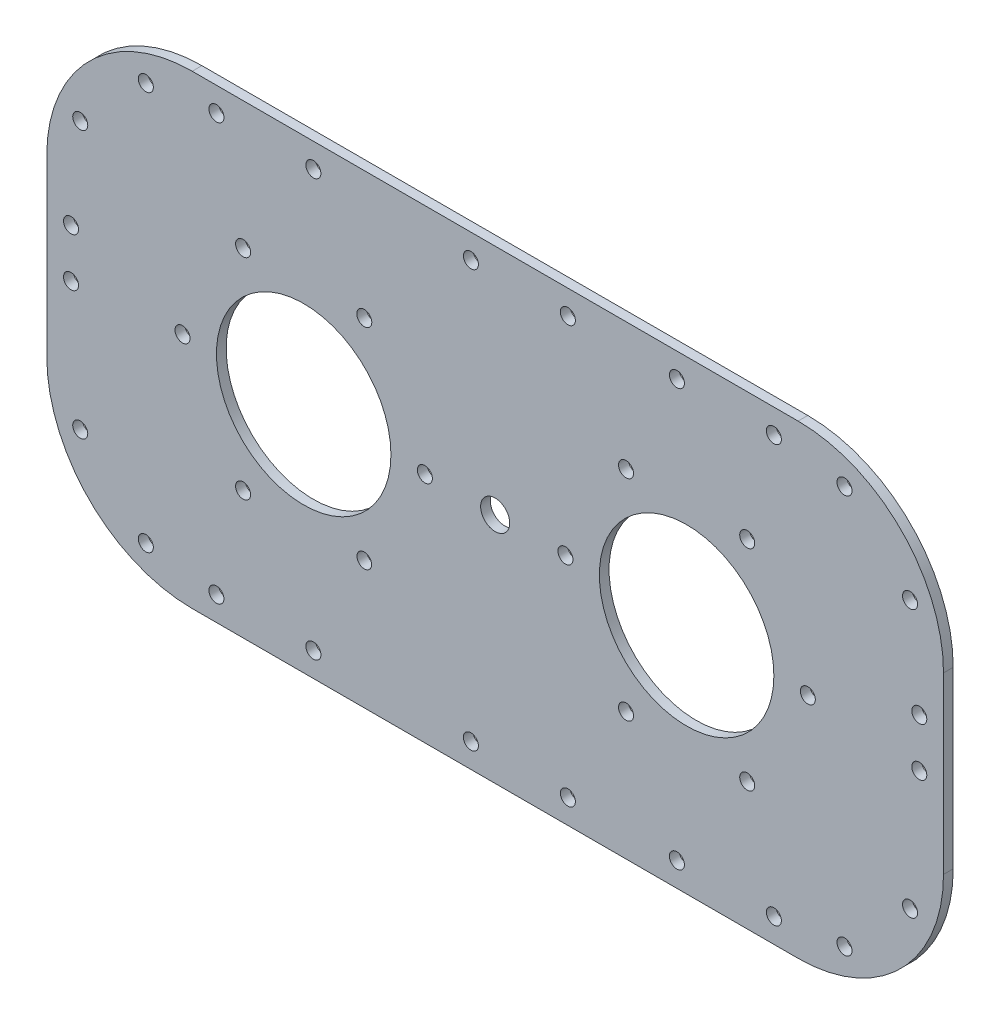
SolidWorks part; units mm, degrees
material "Thornel Mat VMA"
ref_plane "前视基准面" through (0, 0, 0) normal (0, 0, 1) x (1, 0, 0)
ref_plane "上视基准面" through (0, 0, 0) normal (0, 1, 0) x (1, 0, 0)
ref_plane "右视基准面" through (0, 0, 0) normal (1, 0, 0) x (0, 0, -1)
sketch "草图1" plane through (0, 0, 0) normal (0, 0, 1) x (1, 0, 0)
  line L0 (-39.5, 0) -> (39.5, 0) construction
  line L3 (-62.5, 48) -> (62.5, 48)
  line L4 (-92.5, 18) -> (-92.5, -18)
  line L5 (-62.5, -48) -> (62.5, -48)
  line L6 (92.5, 18) -> (92.5, -18)
  line L7 (-92.5, 48) -> (92.5, -48) construction
  line L8 (-92.5, -48) -> (92.5, 48) construction
  line L9 (-39.5, 0) -> (-52, -21.6506) construction
  line L10 (-39.5, 0) -> (-39.5, -25) construction
  line L11 (-52, 21.6506) -> (-27, -21.6506) construction
  line L12 (-39.5, 0) -> (-27, 21.6506) construction
  line L13 (39.5, 0) -> (27, -21.6506) construction
  line L14 (39.5, 0) -> (52, -21.6506) construction
  line L15 (39.5, 0) -> (39.5, -25) construction
  line L16 (39.5, 0) -> (52, 21.6506) construction
  line L17 (27, 21.6506) -> (39.5, 0) construction
  line L18 (39.5, 0) -> (64.5, 0) construction
  line L19 (-83.7132, 39.2132) -> (-62.5, 18) construction
  line L20 (-83.7132, -39.2132) -> (-73.5552, -29.0552) construction
  line L21 (83.7132, -39.2132) -> (62.5, -18) construction
  line L22 (83.7132, 39.2132) -> (66.1506, 21.6506) construction
  line L23 (62.5, -48) -> (62.5, 48) construction
  line L24 (-62.5, -48) -> (-62.5, 48) construction
  line L25 (0, 48) -> (0, -63.7675) construction
  line L26 (72.0671, 41.097) -> (62.5, 18) construction
  line L27 (-20, -40) -> (20, -40) construction
  line L28 (-20, -40) -> (-20, -46) construction
  line L29 (-20, -46) -> (20, -46) construction
  line L30 (20, -40) -> (20, -46) construction
  line L31 (-20, -40) -> (20, -46) construction
  line L32 (-20, -46) -> (20, -40) construction
  line L33 (62.5, 18) -> (85.597, 27.5671) construction
  line L34 (72.0671, -41.097) -> (62.5, -18) construction
  line L35 (62.5, -18) -> (85.597, -27.5671) construction
  line L36 (92.5, -18) -> (62.5, -18) construction
  line L37 (-73.5552, -29.0552) -> (-62.5, -18) construction
  line L38 (-62.5, -18) -> (-92.5, -18) construction
  line L39 (-85.597, -27.5671) -> (-62.5, -18) construction
  line L40 (-62.5, -18) -> (-72.0671, -41.097) construction
  line L41 (-85.597, 27.5671) -> (-62.5, 18) construction
  line L42 (-62.5, 18) -> (-72.0671, 41.097) construction
  circle A16 centre (-39.5, 0) radius 25 construction
  circle A17 centre (39.5, 0) radius 25 construction
  arc A18 (92.5, 18) -> (62.5, 48) centre (62.5, 18) ccw
  arc A19 (92.5, -18) -> (62.5, -48) centre (62.5, -18) cw
  arc A20 (-92.5, -18) -> (-62.5, -48) centre (-62.5, -18) ccw
  arc A21 (-92.5, 18) -> (-62.5, 48) centre (-62.5, 18) cw
  circle A22 centre (-64.5, 0) radius 1.55
  circle A23 centre (-14.5, 0) radius 1.55
  circle A24 centre (14.5, 0) radius 1.55
  circle A25 centre (64.5, 0) radius 1.55
  circle A26 centre (27, 21.6506) radius 1.55
  circle A27 centre (52, 21.6506) radius 1.55
  circle A28 centre (52, -21.6506) radius 1.55
  circle A29 centre (27, -21.6506) radius 1.55
  circle A30 centre (-52, -21.6506) radius 1.55
  circle A33 centre (-52, 21.6506) radius 1.55
  circle A34 centre (-27, -21.6506) radius 1.51
  circle A35 centre (-27, 21.6506) radius 1.55
  circle A48 centre (-39.5, 0) radius 18
  circle A49 centre (39.5, 0) radius 18
  circle A50 centre (57.5, -43) radius 1.55
  circle A51 centre (37.5, -43) radius 1.55
  circle A52 centre (-57.5, -43) radius 1.55
  circle A53 centre (-37.5, -43) radius 1.55
  circle A54 centre (-57.5, 43) radius 1.55
  circle A55 centre (-37.5, 43) radius 1.55
  circle A56 centre (37.5, 43) radius 1.55
  circle A57 centre (57.5, 43) radius 1.55
  circle A58 centre (15, -43) radius 1.55
  circle A59 centre (-5, -43) radius 1.55
  circle A60 centre (-5, 43) radius 1.55
  circle A61 centre (15, 43) radius 1.55
  circle A62 centre (85.597, 27.5671) radius 1.55
  circle A63 centre (72.0671, 41.097) radius 1.55
  circle A64 centre (72.0671, -41.097) radius 1.55
  circle A65 centre (85.597, -27.5671) radius 1.55
  circle A66 centre (-85.597, -27.5671) radius 1.55
  circle A67 centre (-72.0671, -41.097) radius 1.55
  circle A68 centre (-85.597, 27.5671) radius 1.55
  circle A69 centre (-72.0671, 41.097) radius 1.55
  point P0 (0, 0)
  point P9 (0, 0)
  point P51 (-39.5, 0)
  point P77 (0, -43)
  dimension "D2" = 96
  dimension "D4" = 30
  dimension "D5" = 30
  dimension "D6" = 30
  dimension "D8" = 30
  dimension "D12" = 5
  dimension "D20" = 5
  dimension "D16" = 5
  dimension "D30" = 5
  dimension "D32" = 22.5
  dimension "D34" = 25
  dimension "D36" = 22.5
  dimension "D40" = 22.5
  dimension "D44" = 22.5
  dimension "D1" = 79
  dimension "D3" = 185
  dimension "D7" = 60
  dimension "D9" = 30
  dimension "D10" = 60
  dimension "D11" = 60
  dimension "D13" = 5
  dimension "D14" = 20
  dimension "D15" = 5
  dimension "D17" = 20
  dimension "D18" = 5
  dimension "D19" = 5
  dimension "D21" = 20
  dimension "D22" = 5
  dimension "D23" = 5
  dimension "D24" = 5
  dimension "D25" = 5
  dimension "D26" = 5
  dimension "D27" = 20
  dimension "D28" = 40
  dimension "D29" = 6
  dimension "D31" = 20
  dimension "D33" = 22.5
  dimension "D35" = 25
  dimension "D37" = 22.5
  dimension "D38" = 25
  dimension "D39" = 25
  dimension "D41" = 22.5
  dimension "D42" = 25
  dimension "D43" = 25
  dimension "D45" = 22.5
  dimension "D46" = 25
  dimension "D47" = 25
extrude "凸台-拉伸1" add sketch "草图1" along normal blind 2
sketch "草图2" plane through (0, 0, 2) normal (0, 0, 1) x (1, 0, 0)
  line L5 (92.5, -18) -> (92.5, 18) construction
  line L6 (-92.5, 18) -> (-92.5, -18) construction
  line L14 (92.5, 18) -> (59.377, 18) construction
  line L15 (-92.5, 18) -> (-61.0137, 18) construction
  circle A0 centre (87.5, 8) radius 1.55
  circle A1 centre (87.5, -2) radius 1.55
  circle A2 centre (-87.5, 8) radius 1.55
  circle A3 centre (-87.5, -2) radius 1.55
  circle A4 centre (0, 0) radius 3
  dimension "D1" = 10
  dimension "D2" = 10
  dimension "D3" = 10
  dimension "D4" = 10
  dimension "D5" = 5
  dimension "D6" = 5
extrude "切除-拉伸1" cut sketch "草图2" against normal blind 10
